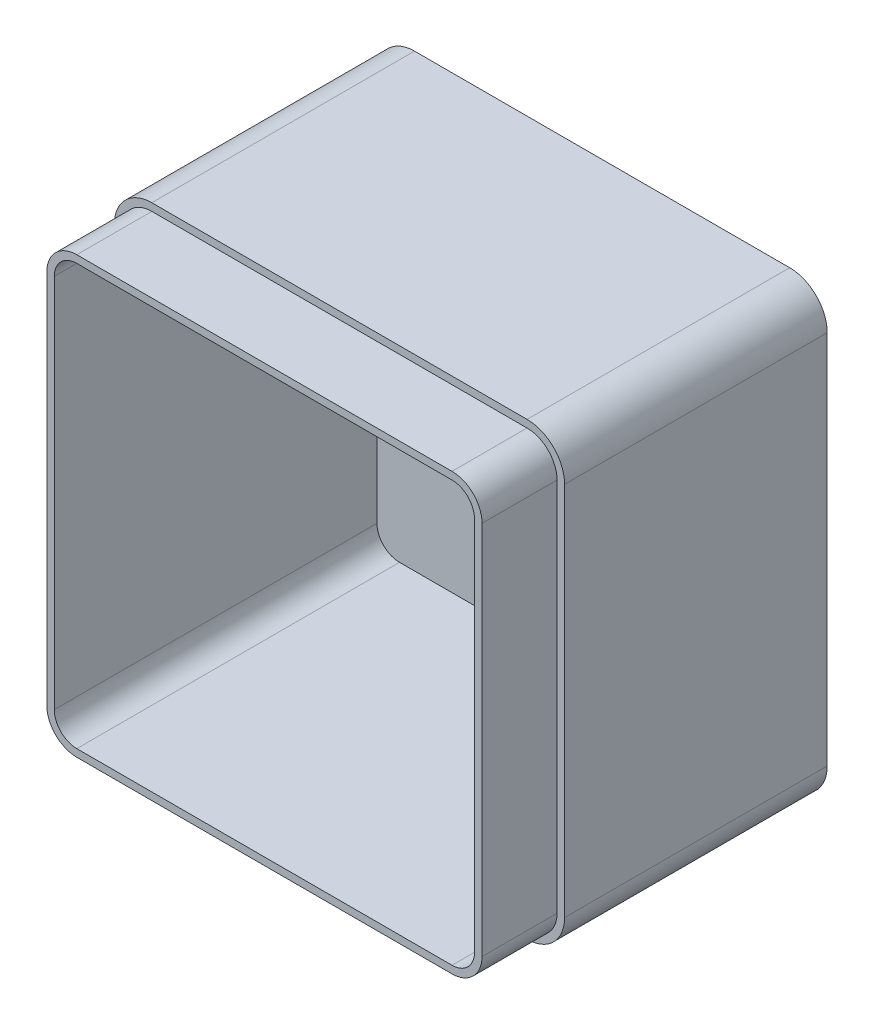
SolidWorks part; units mm, degrees
ref_plane "Front" through (0, 0, 0) normal (0, 0, 1) x (1, 0, 0)
ref_plane "Top" through (0, 0, 0) normal (0, 1, 0) x (1, 0, 0)
ref_plane "Right" through (0, 0, 0) normal (1, 0, 0) x (0, 0, -1)
sketch "Sketch1" plane through (0, 0, 0) normal (0, 0, 1) x (1, 0, 0)
  line L1 (0, 0) -> (120, 0)
  line L2 (0, 0) -> (0, 120)
  line L3 (0, 120) -> (120, 120)
  line L4 (120, 0) -> (120, 120)
  dimension "D1" = 120
  dimension "D2" = 120
extrude "Boss-Extrude1" add sketch "Sketch1" along normal blind 90
fillet "Fillet1" radius 10 4 edges at (120, 0, 45) (0, 0, 45) (0, 120, 45) (120, 120, 45)
shell "Shell3" thickness 4
sketch "Sketch2" plane through (0, 0, 90) normal (0, 0, 1) x (1, 0, 0)
  line L0 (10, 2) -> (110, 2)
  line L1 (118, 10) -> (118, 110)
  line L2 (110, 118) -> (10, 118)
  line L3 (2, 110) -> (2, 10)
  line L4 (10, 0) -> (110, 0)
  line L5 (120, 10) -> (120, 110)
  line L6 (110, 120) -> (10, 120)
  line L7 (0, 110) -> (0, 10)
  line L8 (10, 0) -> (110, 0)
  line L9 (120, 10) -> (120, 110)
  line L10 (110, 120) -> (10, 120)
  line L11 (0, 110) -> (0, 10)
  arc A0 (110, 2) -> (118, 10) centre (110, 10) ccw
  arc A1 (118, 110) -> (110, 118) centre (110, 110) ccw
  arc A2 (10, 118) -> (2, 110) centre (10, 110) ccw
  arc A3 (2, 10) -> (10, 2) centre (10, 10) ccw
  arc A4 (110, 0) -> (120, 10) centre (110, 10) ccw
  arc A5 (120, 110) -> (110, 120) centre (110, 110) ccw
  arc A6 (10, 120) -> (0, 110) centre (10, 110) ccw
  arc A7 (0, 10) -> (10, 0) centre (10, 10) ccw
  arc A8 (110, 0) -> (120, 10) centre (110, 10) ccw
  arc A9 (120, 110) -> (110, 120) centre (110, 110) ccw
  arc A10 (10, 120) -> (0, 110) centre (10, 110) ccw
  arc A11 (0, 10) -> (10, 0) centre (10, 10) ccw
  dimension "D1" = 0
  dimension "D2" = 2
extrude "Cut-Extrude1" cut sketch "Sketch2" against normal blind 20
